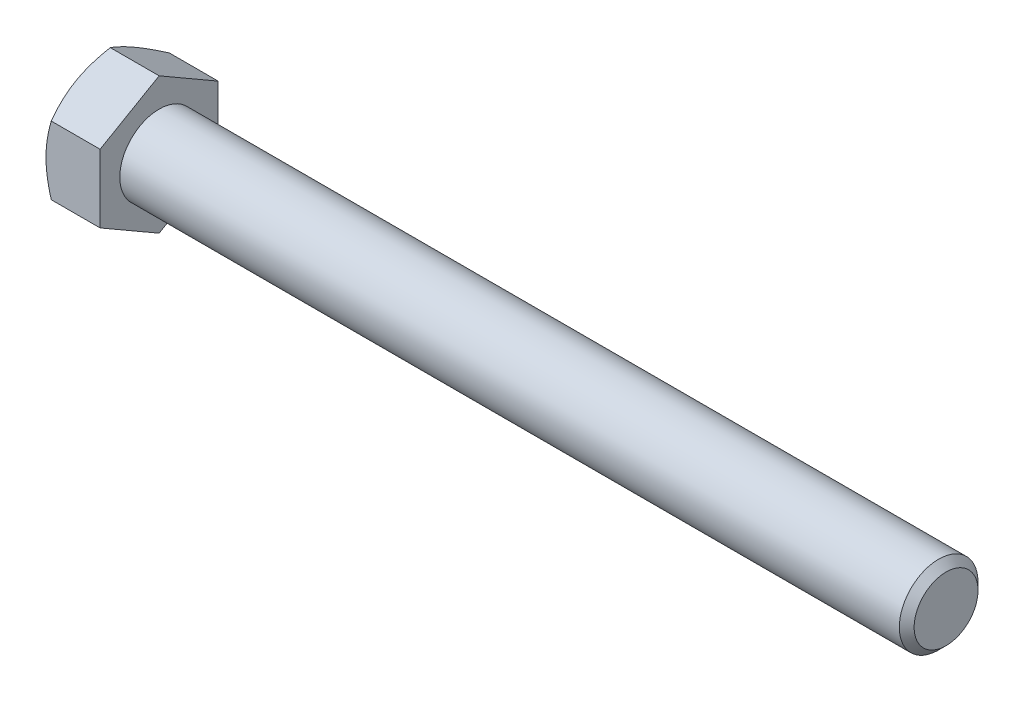
SolidWorks part; units mm, degrees
ref_plane "Front Plane" through (0, 0, 0) normal (0, 0, 1) x (1, 0, 0)
ref_plane "Top Plane" through (0, 0, 0) normal (0, 1, 0) x (1, 0, 0)
ref_plane "Right Plane" through (0, 0, 0) normal (1, 0, 0) x (0, 0, -1)
sketch "Sketch1" plane through (0, 0, 0) normal (0, 0, 1) x (1, 0, 0)
  line L0 (-67.8656, 0) -> (67.8656, 0) construction
  line L1 (67.8656, 6.35) -> (67.8656, -6.35) construction
  line L2 (-59.1344, 9.525) -> (-59.1344, -9.525) construction
  line L3 (-67.8656, 9.525) -> (-67.8656, -9.525) construction
  point P9 (-59.1344, 0)
  point P10 (61.0272, -6.35)
  dimension "Screw Dia" = 12.7
  dimension "Hex" = 19.05
  dimension "Head Ht" = 8.7312
  dimension "Screw Lenght" = 127
  dimension "D1" = 6.8385
ref_plane "Plane2" through (67.8656, 0, 0) normal (1, 0, 0) x (0, 0, -1)
sketch "Sketch5" plane through (67.8656, 0, 0) normal (1, 0, 0) x (0, 0, -1)
  circle A0 centre (0, 0) radius 6.35
extrude "Boss-Extrude3" add sketch "Sketch5" against normal up to vertex (127 mm away) up to point (-59.1344, 0, 0)
sketch "Sketch9" plane through (67.8656, 0, 0) normal (1, 0, 0) x (0, 0, -1)
  circle A1 centre (0, 0) radius 6.35
  circle A2 centre (0, 0) radius 6.35
  dimension "D1" = 0
curve "Helix/Spiral1" pitch 1.9538 height 128.9538 turns 66 parameters "Pitch"=1.9538
chamfer "Chamfer1" distance 1.1958 angle 45 1 edges at (67.8656, 0, -6.35)
sketch "Sketch10" plane through (0, 0, 0) normal (0, 0, 1) x (1, 0, 0)
  line L0 (67.8656, 6.35) -> (68.5983, 5.0809)
  line L1 (68.5983, 5.0809) -> (68.8425, 5.0809)
  line L2 (68.8425, 5.0809) -> (69.5752, 6.35)
  line L3 (67.8656, 6.35) -> (69.5752, 6.35)
  line L4 (68.7204, 6.35) -> (68.7204, 5.0809) construction
  line L5 (68.232, 5.7155) -> (69.2089, 5.7155) construction
  dimension "D1" = 60
  dimension "D2" = 0.2442
  dimension "D3" = 0.9769
sketch "Sketch6" plane through (-59.1344, 0, 0) normal (-1, 0, 0) x (0, 0, 1)
  line L0 (0, 9.525) -> (0, -9.525) construction
  line L1 (9.525, 5.4993) -> (0, 10.9985)
  line L2 (0, 10.9985) -> (-9.525, 5.4993)
  line L3 (-9.525, 5.4993) -> (-9.525, -5.4993)
  line L4 (-9.525, -5.4993) -> (0, -10.9985)
  line L5 (0, -10.9985) -> (9.525, -5.4993)
  line L6 (9.525, -5.4993) -> (9.525, 5.4993)
  circle A0 centre (0, 0) radius 9.525 construction
extrude "Boss-Extrude4" add sketch "Sketch6" along normal up to vertex (8.7312 mm away) up to point (-67.8656, -9.525, 0)
sketch "Sketch7" plane through (-67.8656, 0, 0) normal (-1, 0, 0) x (0, 0, 1)
  circle A0 centre (0, 0) radius 9.525 construction
  circle A1 centre (0, 0) radius 9.525
sketch "Sketch8" plane through (-67.8656, 0, 0) normal (-1, 0, 0) x (0, 0, 1)
  circle A0 centre (0, 0) radius 9.525 construction
  circle A1 centre (0, 0) radius 9.525
extrude "Cut-Extrude3" cut sketch "Sketch8" against normal through all draft 60 flip side to cut
sketch "Sketch12" plane through (-67.8656, 0, 0) normal (-1, 0, 0) x (0, 0, 1)
  line L0 (0, 7.3343) -> (0, 4.0958) construction
  line L1 (0.2858, 7.3343) -> (0.2858, 4.0958)
  line L2 (-0.2858, 7.3343) -> (-0.2857, 4.0958)
  line L3 (0, 6.35) -> (0, -6.35) construction
  arc A0 (0.2858, 7.3343) -> (-0.2858, 7.3343) centre (0, 7.3343) ccw
  arc A1 (-0.2857, 4.0958) -> (0.2858, 4.0958) centre (0, 4.0958) ccw
  circle A3 centre (0, 0) radius 3.81 construction
  circle A4 centre (0, 0) radius 7.62 construction
  point P2 (0, 5.715)
  dimension "D1" = 7.62
  dimension "D3" = 15.24
  dimension "D2" = 0.5715
extrude "Cut-Extrude4" cut sketch "Sketch12" against normal blind 0.254
pattern_circular "CirPattern1" count 3 over 360 about axis through (0, 0, 0) along (1, 0, 0) of "Cut-Extrude4"
equation "\"D2@Sketch10\" = \"Pitch@Helix/Spiral1\"*.125"
equation "\"D3@Sketch10\" = \"Pitch@Helix/Spiral1\"*.5"
equation "\"D1@Chamfer1\" = \"Pitch@Helix/Spiral1\"*.612"
equation "\"D1@Sketch12\" = \"Hex@Sketch1\"*.4"
equation "\"D3@Sketch12\" = \"Hex@Sketch1\"*.8"
equation "\"D2@Sketch12\" = \"Hex@Sketch1\"*.03"
equation "\"D1@Sketch1\" = \"Pitch@Helix/Spiral1\"*3.5"
equation "\"D3@Helix/Spiral1\" = \"Screw Lenght@Sketch1\"+\"Pitch@Helix/Spiral1\""
